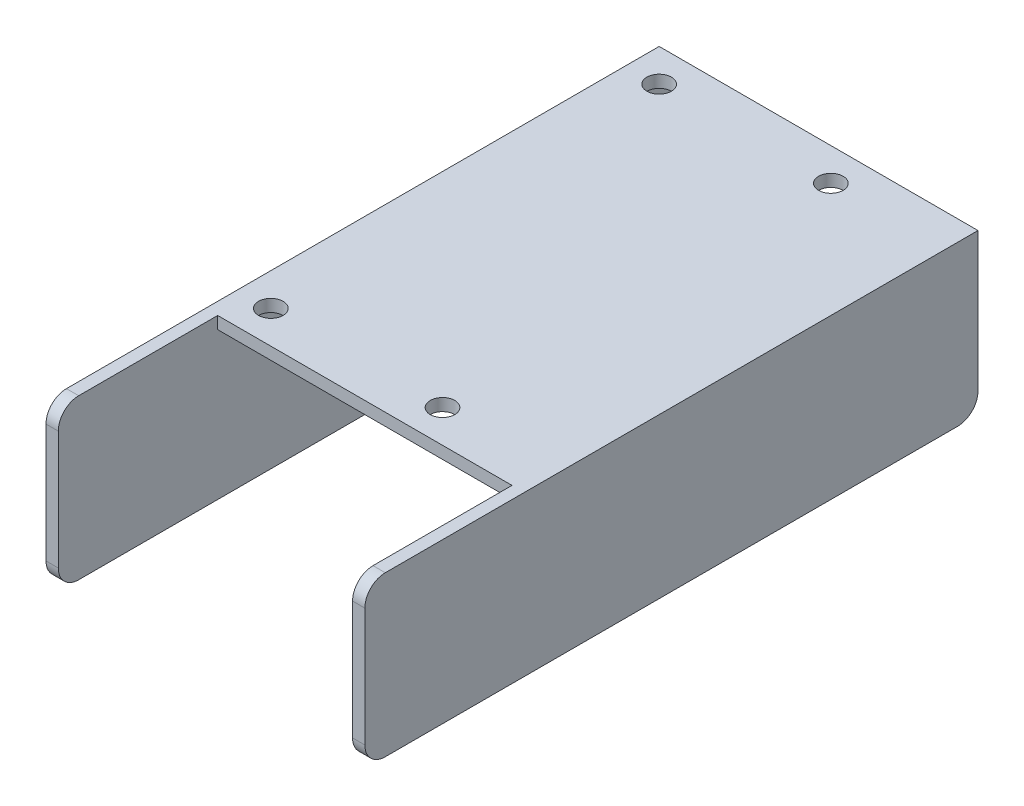
SolidWorks part; units mm, degrees
ref_plane "Front Plane" through (0, 0, 0) normal (0, 0, 1) x (1, 0, 0)
ref_plane "Top Plane" through (0, 0, 0) normal (0, 1, 0) x (1, 0, 0)
ref_plane "Right Plane" through (0, 0, 0) normal (1, 0, 0) x (0, 0, -1)
sketch "Sketch1" plane through (0, 0, 0) normal (0, 1, 0) x (1, 0, 0)
  line L0 (0, -36) -> (0, -75)
  line L1 (0, 0) -> (-75, 0) construction
  line L2 (0, 0) -> (0, 75)
  line L3 (0, 0) -> (75, 0) construction
  line L4 (0, 75) -> (-39, 75)
  line L5 (-39, 75) -> (-39, -75)
  line L6 (-39, -75) -> (-36, -75)
  line L7 (-36, -75) -> (-36, -36) construction
  line L8 (-36, -36) -> (0, -36) construction
  line L9 (0, 0) -> (0, -36)
  line L10 (-39, 19.5) -> (0, 19.5) construction
  line L11 (-36, -75) -> (0, -75)
  circle A0 centre (-31, 67) radius 3 construction
  circle A1 centre (-31, -28) radius 3 construction
  point P9 (0, 0)
  dimension "D9" = 6
  dimension "D2" = 39
  dimension "D3" = 111
  dimension "D4" = 39
  dimension "D5" = 3
  dimension "D6" = 75
  dimension "D7" = 8
  dimension "D8" = 8
  dimension "D10" = 55.5
  dimension "D11" = 150
  dimension "D1" = 4
extrude "Boss-Extrude1" add sketch "Sketch1" along normal mid plane 39
mirror "Mirror1" about plane through (0, 0, 0) normal (1, 0, 0) of "Boss-Extrude1"
shell "Shell1" thickness 3
sketch "Sketch2" plane through (0, 19.5, 0) normal (0, 1, 0) x (1, 0, 0)
  line L0 (-36, -75) -> (-36, -36) construction
  line L1 (-36, -36) -> (0, -36) construction
  line L2 (0, -36) -> (0, -75) construction
  line L3 (-36, -75) -> (0, -75) construction
  line L4 (-36, -75) -> (-36, -36)
  line L5 (-36, -36) -> (0, -36)
  line L6 (0, -36) -> (0, -75)
  line L7 (-36, -75) -> (0, -75)
  circle A0 centre (-31, -28) radius 3 construction
  circle A1 centre (-31, 67) radius 3 construction
  circle A2 centre (-31, -28) radius 3 construction
  circle A3 centre (-31, 67) radius 3 construction
extrude "Cut-Extrude1" cut sketch "Sketch2" against normal up to next (3 mm away)
mirror "Mirror2" about plane through (0, 0, 0) normal (1, 0, 0) of "Cut-Extrude1"
fillet "Fillet1" radius 5 4 edges at (-37.5, -19.5, -75) (37.5, -19.5, -75) (37.5, -19.5, 75) (37.5, 19.5, 75)
sketch "Sketch3" plane through (0, 19.5, 0) normal (0, 1, 0) x (1, 0, 0)
  circle A0 centre (-31, 67) radius 3 construction
  circle A1 centre (-31, -28) radius 3 construction
  circle A2 centre (-31, 67) radius 3
  circle A3 centre (-31, -28) radius 3
  circle A4 centre (11, -28) radius 3
  circle A5 centre (11, 67) radius 3
  dimension "D2" = 42
  dimension "D1" = 2
extrude "Cut-Extrude2" cut sketch "Sketch3" against normal up to next
equation "\"D6@Sketch1\"=(\"D3@Sketch1\"+\"D4@Sketch1\")/2"
equation "\"D10@Sketch1\"=\"D3@Sketch1\"/2"
